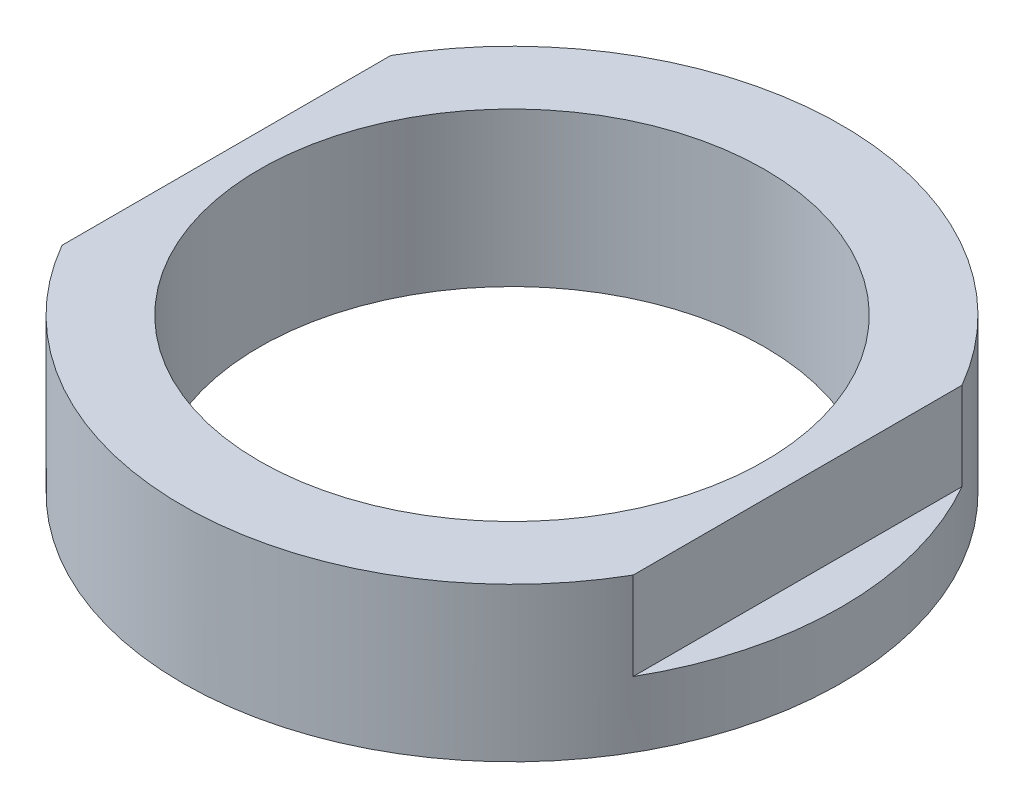
SolidWorks part; units mm, degrees
other "Body_Thread"
ref_plane "Front Plane" through (0, 0, 0) normal (0, 0, 1) x (1, 0, 0)
ref_plane "Top Plane" through (0, 0, 0) normal (0, 1, 0) x (1, 0, 0)
ref_plane "Right Plane" through (0, 0, 0) normal (1, 0, 0) x (0, 0, -1)
sketch "Sketch1" plane through (0, 0, 0) normal (0, 1, 0) x (1, 0, 0)
  circle A0 centre (0, 0) radius 15
  dimension "D1" = 30
extrude "Body" add sketch "Sketch1" along normal blind 7
sketch "Sketch2" plane through (0, 7, 0) normal (0, 1, 0) x (1, 0, 0)
  circle A0 centre (0, 0) radius 11.5
  dimension "D1" = 23
extrude "Center_hole" cut sketch "Sketch2" against normal blind 18
sketch "Sketch4" plane through (0, 7, 0) normal (0, 1, 0) x (1, 0, 0)
  line L0 (-55, 0) -> (55, 0) construction
  line L5 (17, -9.4158) -> (13, -9.4158)
  line L6 (17, -9.4158) -> (17, 9.4158)
  line L7 (17, 9.4158) -> (13, 9.4158)
  line L8 (13, -9.4158) -> (13, 9.4158)
  line L9 (17, -9.4158) -> (13, 9.4158) construction
  line L10 (17, 9.4158) -> (13, -9.4158) construction
  line L11 (0, 18.2306) -> (0, -17.8299) construction
  line L12 (-17, 9.4158) -> (-13, 9.4158)
  line L13 (-13, -9.4158) -> (-13, 9.4158)
  line L14 (-17, -9.4158) -> (-13, -9.4158)
  line L15 (-17, -9.4158) -> (-17, 9.4158)
  circle A0 centre (0, 0) radius 15 construction
  point P0 (15, 0)
  dimension "D1" = 4
extrude "Hex" cut sketch "Sketch4" against normal blind 4
